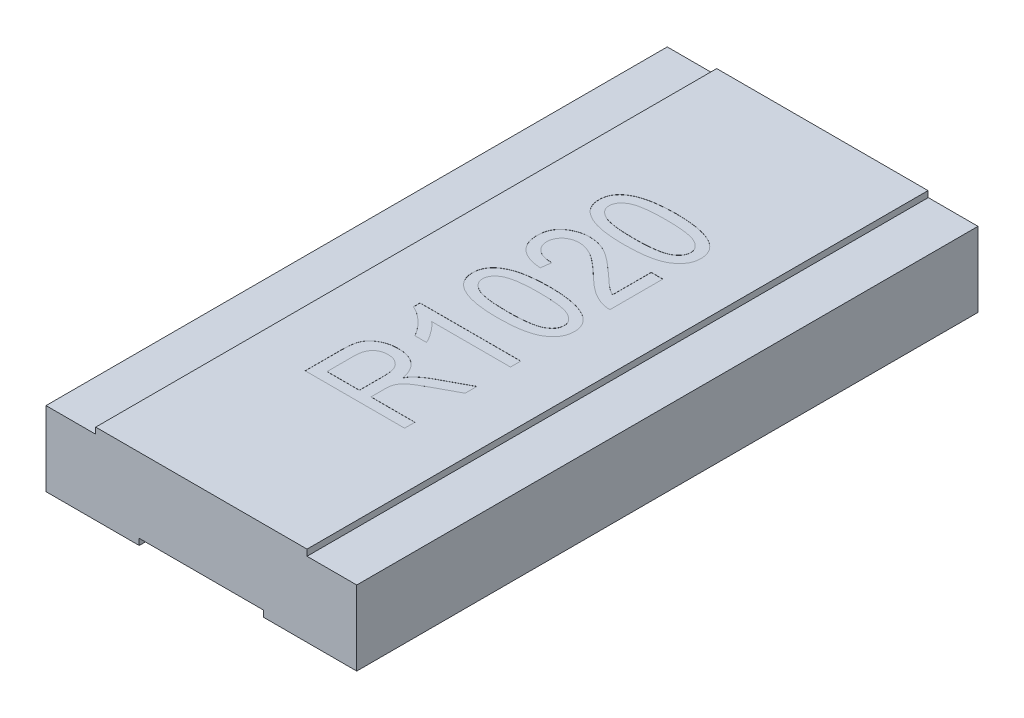
SolidWorks part; units mm, degrees
ref_plane "Front Plane" through (0, 0, 0) normal (0, 0, 1) x (1, 0, 0)
ref_plane "Top Plane" through (0, 0, 0) normal (0, 1, 0) x (1, 0, 0)
ref_plane "Right Plane" through (0, 0, 0) normal (1, 0, 0) x (0, 0, -1)
sketch "Sketch1" plane through (0, 0, 0) normal (0, 0, 1) x (1, 0, 0)
  line L0 (0, -50) -> (0, 50) construction
  line L1 (-1.2, 0) -> (1.2, 0)
  line L2 (-1.2, 0) -> (-1.2, 0.5)
  line L3 (-1.2, 0.5) -> (1.2, 0.5)
  line L4 (1.2, 0) -> (1.2, 0.5)
  line L5 (-1.2, 0) -> (1.2, 0.5) construction
  line L6 (-1.2, 0.5) -> (1.2, 0) construction
  line L7 (50, 0) -> (-50, 0) construction
  point P0 (0, 0)
  point P6 (0, 0)
  point P7 (0, 0)
  point P8 (0, 0)
  dimension "D1" = 2.4
  dimension "D2" = 0.5
extrude "Boss-Extrude1" add sketch "Sketch1" along normal mid plane 5
ref_plane "Plane1" through (0, 0, 0.001) normal (0, 0, 1) x (1, 0, 0)
sketch "Sketch4" plane through (0, 0, 0.001) normal (0, 0, 1) x (1, 0, 0)
  line L0 (-0.85, 0.5) -> (-1.2, 0.5)
  line L1 (1.2, 0.5) -> (-1.2, 0.5) construction
  line L2 (-1.2, 0.5) -> (-1.2, 0)
  line L3 (-1.2, 0) -> (-0.5, 0)
  line L4 (-1.2, 0) -> (1.2, 0) construction
  line L5 (-0.85, 0.55) -> (-1.25, 0.55)
  line L6 (-1.25, 0.55) -> (-1.25, -0.05)
  line L7 (-1.25, -0.05) -> (-0.5, -0.05)
  line L8 (-0.85, 0.55) -> (-0.85, 0.5)
  line L9 (-0.5, 0) -> (-0.5, -0.05)
  line L10 (0, 0.5) -> (0, 0) construction
  line L11 (0.5, 0) -> (0.5, -0.05)
  line L12 (0.85, 0.55) -> (0.85, 0.5)
  line L13 (1.25, -0.05) -> (0.5, -0.05)
  line L14 (1.25, 0.55) -> (1.25, -0.05)
  line L15 (0.85, 0.55) -> (1.25, 0.55)
  line L16 (1.2, 0) -> (0.5, 0)
  line L17 (1.2, 0.5) -> (1.2, 0)
  line L18 (0.85, 0.5) -> (1.2, 0.5)
  dimension "D1" = 0.35
  dimension "D2" = 0.7
  dimension "D3" = 0.05
extrude "Boss-Extrude4" add sketch "Sketch4" along normal mid plane 4.998
ref_plane "Plane2" through (0, 0, 0.002) normal (0, 0, 1) x (1, 0, 0)
sketch "Sketch6" plane through (0, 0, 0.002) normal (0, 0, 1) x (1, 0, 0)
  line L1 (-0.85, 0.5) -> (0.85, 0.5)
  line L2 (-0.85, 0.5) -> (-0.85, 0.6)
  line L3 (-0.85, 0.6) -> (0.85, 0.6)
  line L4 (0.85, 0.5) -> (0.85, 0.6)
  dimension "D1" = 0.1
extrude "Boss-Extrude6" add sketch "Sketch6" along normal mid plane 4.996
sketch "Sketch7" plane through (0, 0.6, 0) normal (0, 1, 0) x (1, 0, 0)
  line L0 (0.4, -1.3378) -> (0.4, 1.3065) construction
  line L1 (0, -50) -> (0, 50) construction
  text T0 "R1020" font "Arial Narrow" height 0.8
  dimension "D1" = 0.4
extrude "Cut-Extrude1" cut sketch "Sketch7" against normal blind 0.001
